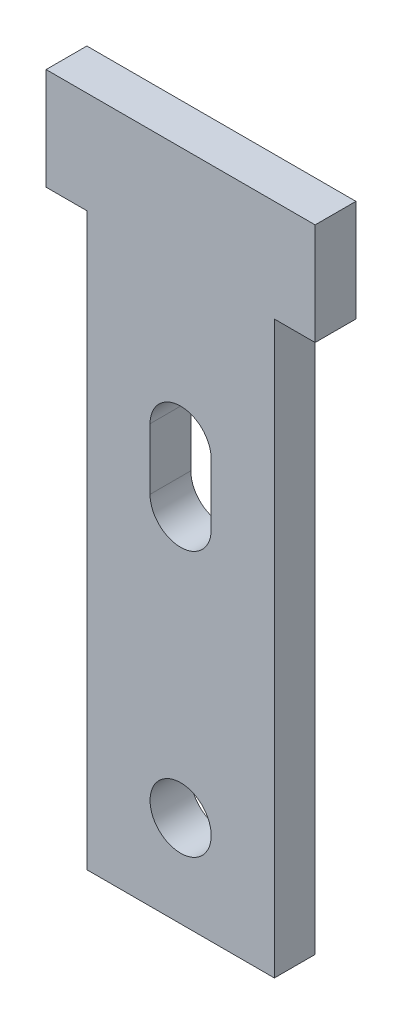
SolidWorks part; units mm, degrees
ref_plane "Front Plane" through (0, 0, 0) normal (0, 0, 1) x (1, 0, 0)
ref_plane "Top Plane" through (0, 0, 0) normal (0, 1, 0) x (1, 0, 0)
ref_plane "Right Plane" through (0, 0, 0) normal (1, 0, 0) x (0, 0, -1)
sketch "Sketch1" plane through (0, 0, 0) normal (0, 1, 0) x (1, 0, 0)
  line L1 (-5.842, -1.27) -> (5.842, -1.27)
  line L2 (-5.842, -1.27) -> (-5.842, 1.27)
  line L3 (-5.842, 1.27) -> (5.842, 1.27)
  line L4 (5.842, -1.27) -> (5.842, 1.27)
  line L5 (-5.842, -1.27) -> (5.842, 1.27) construction
  line L6 (-5.842, 1.27) -> (5.842, -1.27) construction
  point P0 (0, 0)
  dimension "D1" = 2.54
  dimension "D2" = 11.684
extrude "Boss-Extrude1" add sketch "Sketch1" along normal blind 35.56
sketch "Sketch2" plane through (0, 0, 1.27) normal (0, 0, 1) x (1, 0, 0)
  line L0 (-5.842, 35.56) -> (5.842, 35.56) construction
  line L1 (-5.842, 35.56) -> (5.842, 35.56)
  line L2 (0, 35.56) -> (0, 7.0568) construction
  line L3 (5.842, 35.56) -> (8.382, 35.56)
  line L4 (8.382, 35.56) -> (8.382, 41.91)
  line L5 (-8.382, 35.56) -> (-8.382, 41.91)
  line L6 (-5.842, 35.56) -> (-8.382, 35.56)
  line L7 (-8.382, 41.91) -> (8.382, 41.91)
  line M10 (5.842, 35.56) -> (-5.842, 35.56)
  dimension "D1" = 2.54
  dimension "D2" = 6.35
extrude "Boss-Extrude2" add sketch "Sketch2" against normal up to surface (2.54 mm away) contours L7 L5 L6 L1 L3 L4 M10 up to face at (0, 17.78, -1.27)
sketch "Sketch3" plane through (0, 0, 1.27) normal (0, 0, 1) x (1, 0, 0)
  line L0 (0, 0) -> (0, 3.81) construction
  line L1 (0, 7.62) -> (0, 20.32) construction
  line L2 (0, 26.035) -> (0, 22.225) construction
  line L3 (1.905, 26.035) -> (1.905, 22.225)
  line L4 (-1.905, 26.035) -> (-1.905, 22.225)
  circle A0 centre (0, 5.715) radius 1.905
  arc A1 (1.905, 26.035) -> (-1.905, 26.035) centre (0, 26.035) ccw
  arc A2 (-1.905, 22.225) -> (1.905, 22.225) centre (0, 22.225) ccw
  point P9 (0, 24.13)
  point P14 (0, 27.94)
  point P15 (0, 20.32)
  point P16 (-33.9044, 32.0848)
  dimension "D2" = 3.81
  dimension "D1" = 3.81
  dimension "D3" = 12.7
  dimension "D4" = 7.62
extrude "Cut-Extrude1" cut sketch "Sketch3" against normal up to next
